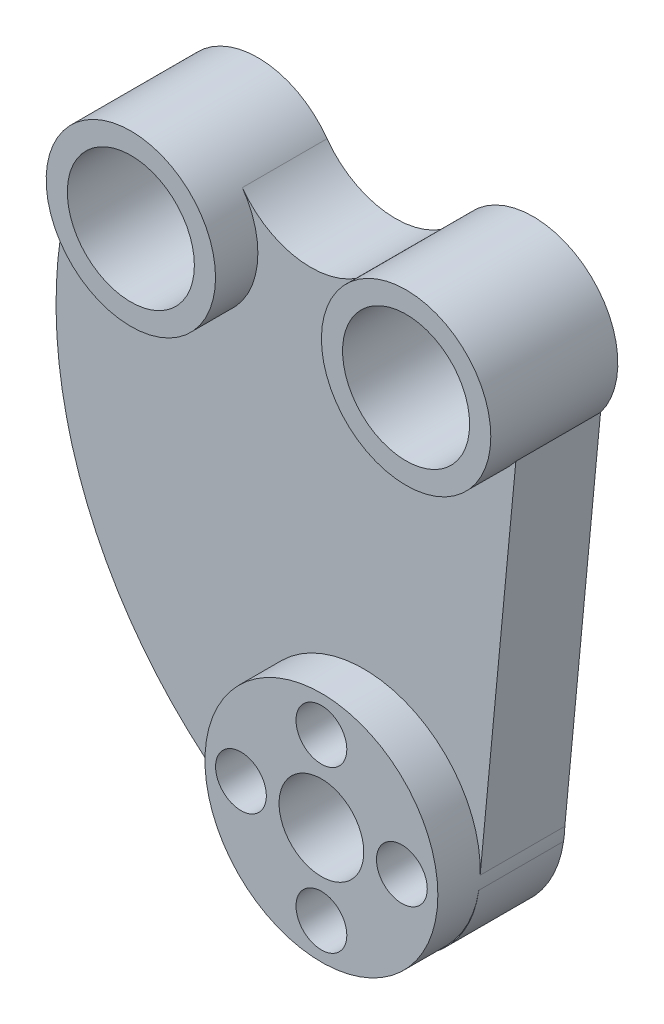
SolidWorks part; units mm, degrees
ref_plane "Front Plane" through (0, 0, 0) normal (0, 0, 1) x (1, 0, 0)
ref_plane "Top Plane" through (0, 0, 0) normal (0, 1, 0) x (1, 0, 0)
ref_plane "Right Plane" through (0, 0, 0) normal (1, 0, 0) x (0, 0, -1)
sketch "Sketch1" plane through (0, 0, 0) normal (0, 0, 1) x (1, 0, 0)
  circle A0 centre (0, 0) radius 10
  circle A1 centre (0, 0) radius 19
  circle A2 centre (0, 0) radius 27.5
  dimension "D1" = 20
  dimension "D2" = 38
  dimension "D3" = 55
extrude "Boss-Extrude1" add sketch "Sketch1" along normal blind 30 contours A2 A1 | A1 A0
sketch "Sketch2" plane through (0, 0, 0) normal (0, 0, 1) x (1, 0, 0)
  line L0 (0, 0) -> (0, 100) construction
  line L1 (0, 100) -> (-45, 100) construction
  line L2 (-45, 100) -> (20, 100) construction
  circle A0 centre (-45, 100) radius 15
  circle A1 centre (-45, 100) radius 20
  circle A2 centre (20, 100) radius 15
  circle A3 centre (20, 100) radius 20
  dimension "D4" = 30
  dimension "D5" = 40
  dimension "D1" = 100
  dimension "D2" = 45
  dimension "D3" = 65
extrude "Boss-Extrude2" add sketch "Sketch2" along normal blind 30 separate body
sketch "Sketch5" plane through (0, 0, 0) normal (0, 0, 1) x (1, 0, 0)
  line L0 (0, -27.5) -> (0, 27.5) construction
  line L1 (27.5, 0) -> (-27.5, 0) construction
  arc A0 (-5.6943, -26.904) -> (-62.9629, 108.794) centre (25.2412, 66.0852) cw
  circle A1 centre (0, 0) radius 27.5 construction
  circle A2 centre (-45, 100) radius 20 construction
  arc A3 (-31.3176, 114.5874) -> (6.3176, 114.5874) centre (-12.5, 121.3622) ccw
  circle A4 centre (20, 100) radius 20 construction
  circle A5 centre (0, 0) radius 19
  circle A6 centre (0, 19) radius 6
  circle A7 centre (-19, 0) radius 6
  circle A8 centre (0, -19) radius 6
  circle A9 centre (19, 0) radius 6
  dimension "D1" = 98
  dimension "D2" = 20
  dimension "D3" = 38
  dimension "D4" = 12
extrude "Cut-Extrude1" cut sketch "Sketch5" along normal blind 30 contours A6 | A9 | A8 | A7
sketch "Sketch6" plane through (0, 0, 0) normal (0, 0, 1) x (1, 0, 0)
  line L0 (35.9146, 87.8869) -> (27.1764, -4.2062)
  arc A0 (-9.3942, -25.8457) -> (-61.3234, 111.5563) centre (25.3358, 65.794) cw
  circle A1 centre (0, 0) radius 27.5 construction
  circle A2 centre (-45, 100) radius 20 construction
  arc A3 (-28.6766, 111.5563) -> (3.6766, 111.5563) centre (-12.5, 123.3171) ccw
  circle A4 centre (20, 100) radius 20 construction
  circle A5 centre (20, 100) radius 20 construction
  circle A6 centre (0, 0) radius 27.5 construction
  arc A7 (-61.3234, 111.5563) -> (-28.6766, 111.5563) centre (-45, 99.6888) cw
  arc A8 (3.6766, 111.5563) -> (35.9146, 87.8869) centre (19.851, 99.7971) cw
  arc A9 (27.1764, -4.2062) -> (-9.3942, -25.8457) centre (0.2444, -0.413) cw
  dimension "D1" = 98
  dimension "D2" = 20
extrude "Boss-Extrude3" add sketch "Sketch6" along normal blind 20
sketch "Sketch7" plane through (0, 0, 20) normal (0, 0, 1) x (1, 0, 0)
  circle A0 centre (-45, 100) radius 15
  circle A1 centre (20, 100) radius 15
  circle A2 centre (0, 19) radius 6
  circle A3 centre (-19, 0) radius 6
  circle A4 centre (0, -19) radius 6
  circle A5 centre (19, 0) radius 6
  circle A6 centre (0, 0) radius 10
extrude "Cut-Extrude2" cut sketch "Sketch7" against normal through all and the other way through all
